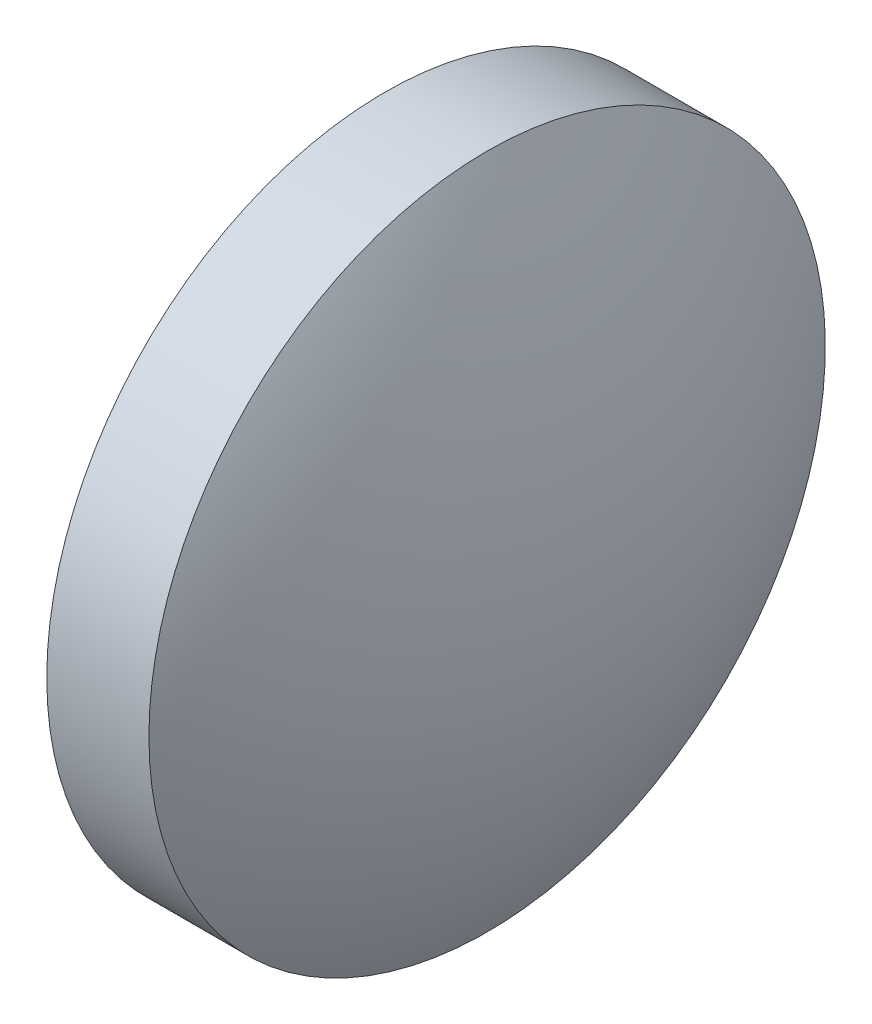
SolidWorks part; units mm, degrees
ref_plane "前视基准面" through (0, 0, 0) normal (0, 0, 1) x (1, 0, 0)
ref_plane "上视基准面" through (0, 0, 0) normal (0, 1, 0) x (1, 0, 0)
ref_plane "右视基准面" through (0, 0, 0) normal (1, 0, 0) x (0, 0, -1)
sketch "草图1" plane through (0, 0, 0) normal (0, 0, 1) x (1, 0, 0)
  line L0 (649.6605, 189.5628) -> (655.7958, 189.5628) construction
  line L1 (650.602, 189.5628) -> (650.602, 194.5628)
  line L2 (653.402, 189.5628) -> (650.602, 189.5628)
  line L5 (650.602, 194.5628) -> (652.112, 194.5628)
  arc A0 (653.402, 189.5628) -> (652.112, 194.5628) centre (643.0671, 189.5628) ccw
revolve "旋转1" add sketch "草图1" angle 360 about L0
